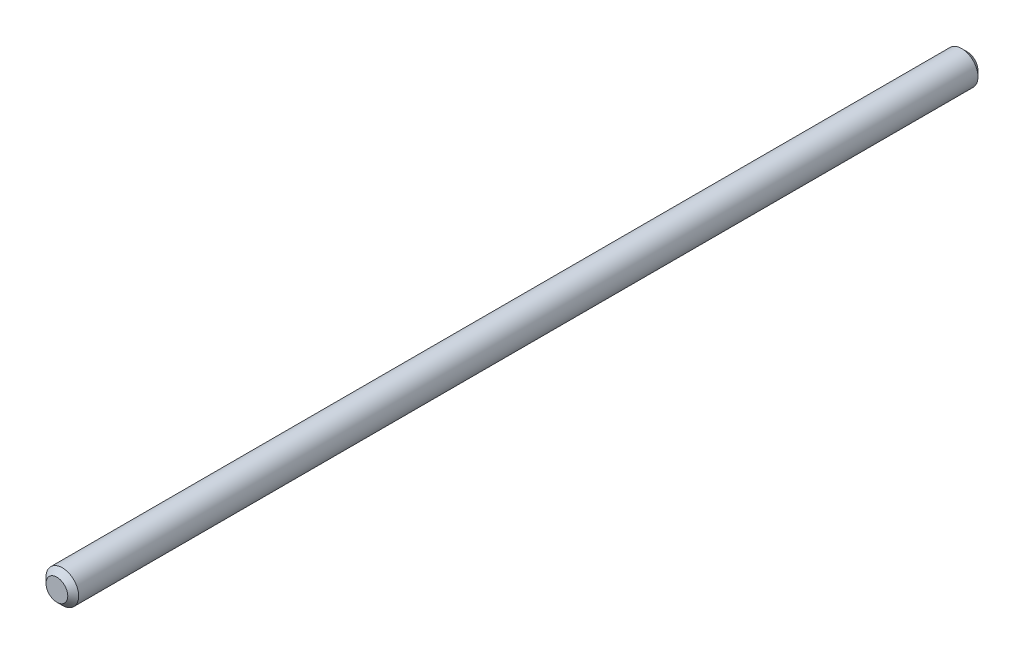
SolidWorks part; units mm, degrees
ref_plane "Face" through (0, 0, 0) normal (0, 0, 1) x (1, 0, 0)
ref_plane "Dessus" through (0, 0, 0) normal (0, 1, 0) x (1, 0, 0)
ref_plane "Droite" through (0, 0, 0) normal (1, 0, 0) x (0, 0, -1)
sketch "Esquisse1" plane through (0, 0, 0) normal (0, 0, 1) x (1, 0, 0)
  circle A0 centre (0, 0) radius 1.5
extrude "Base-Extrusion" add sketch "Esquisse1" along normal blind 83.6
chamfer "Chanfrein1" distance 0.5 angle 45 2 edges at (1.5, 0, 0) (1.5, 0, 83.6)
